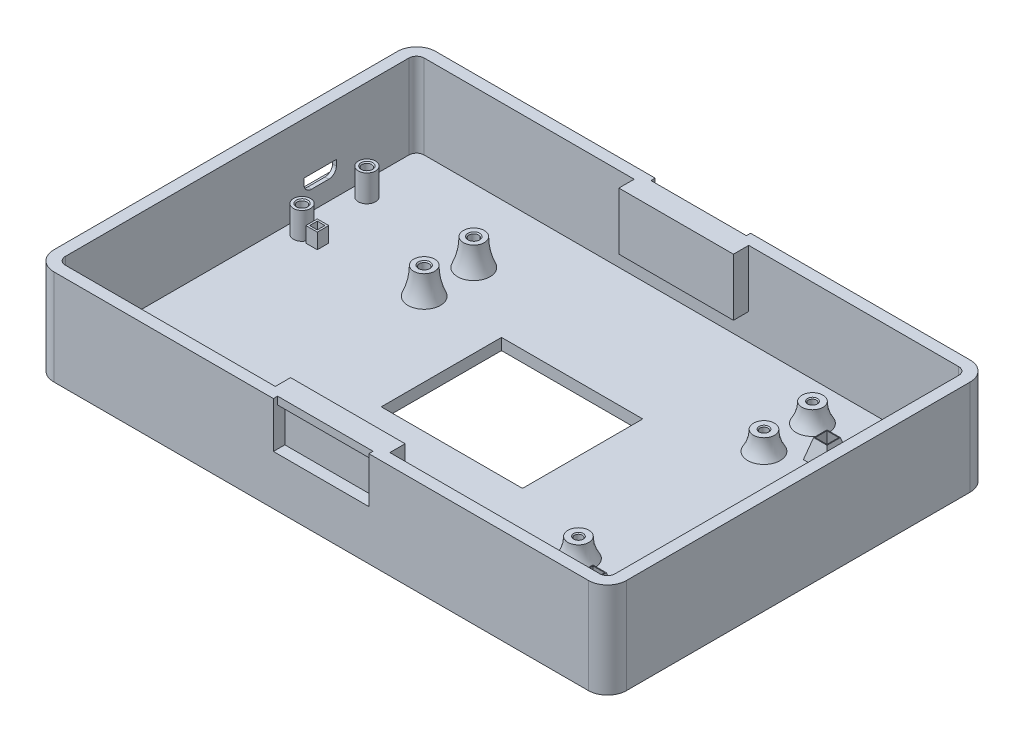
SolidWorks part; units mm, degrees
ref_plane "Front Plane" through (0, 0, 0) normal (0, 0, 1) x (1, 0, 0)
ref_plane "Top Plane" through (0, 0, 0) normal (0, 1, 0) x (1, 0, 0)
ref_plane "Right Plane" through (0, 0, 0) normal (1, 0, 0) x (0, 0, -1)
sketch "Sketch1" plane through (0, 0, 0) normal (0, 1, 0) x (1, 0, 0)
  line L1 (-75, -50) -> (75, -50)
  line L2 (-75, -50) -> (-75, 50)
  line L3 (-75, 50) -> (75, 50)
  line L4 (75, -50) -> (75, 50)
  point P4 (0, 50)
  point P6 (-75, 0)
  dimension "D1" = 100
  dimension "D2" = 150
extrude "Boss-Extrude1" add sketch "Sketch1" along normal blind 25
fillet "Fillet1" radius 5 4 edges at (75, 12.5, -50) (75, 12.5, 50) (-75, 12.5, 50) (-75, 12.5, -50)
shell "Shell2" thickness 3
sketch "Sketch4" plane through (0, 3, 0) normal (0, 1, 0) x (1, 0, 0)
  line L0 (41.7, 24.3) -> (62, 37) construction
  line L1 (41.7, 37) -> (62, 24.3) construction
  line L2 (62, 24.3) -> (62, 37) construction
  line L3 (62, 37) -> (41.7, 37) construction
  line L4 (41.7, 37) -> (41.7, 24.3) construction
  line L5 (41.7, 24.3) -> (62, 24.3) construction
  line L7 (70, 47) -> (-70, 47) construction
  line L8 (72, -45) -> (72, 45) construction
  circle A0 centre (62, 37) radius 2.25
  circle A1 centre (41.7, 37) radius 2.25
  circle A2 centre (41.7, 24.3) radius 2.25
  circle A3 centre (62, 24.3) radius 2.25
  dimension "D1" = 4.5
  dimension "D2" = 12.7
  dimension "D3" = 20.3
  dimension "D4" = 10
  dimension "D5" = 10
extrude "Boss-Extrude4" add sketch "Sketch4" along normal blind 5
hole_wizard "M2.5x0.45 Tapped Hole5" positions "Sketch11" profile "Sketch12" tap size "M2.5x0.45" standard "ANSI Metric"
sketch "Sketch11" plane through (0, 8, 0) normal (0, 1, 0) x (1, 0, 0)
  point P0 (41.7, 37)
  point P3 (62, 24.3)
  point P6 (62, 37)
  point P9 (41.7, 24.3)
sketch "Sketch12" plane through (41.7, 8, -37) normal (1, 0, 0) x (0, 0, 1)
  line L0 (0, 0) -> (0, 5.6159)
  line L1 (0, 5.6159) -> (1.025, 5)
  line L2 (1.025, 5) -> (1.025, 0.25)
  line L3 (1.025, 0.25) -> (1.275, 0)
  line L5 (1.275, 0) -> (0, 0)
  line L6 (-1.025, 0.25) -> (-1.275, 0) construction
  line L10 (0, 5.6159) -> (-1.025, 5) construction
  line L11 (0, -6.35) -> (0, 107.95) construction
  dimension "Tap Drill Dia." = 2.05
  dimension "Tap Drill Depth" = 5
  dimension "Near C'Sink Dia." = 2.55
  dimension "Near C'Sink Angle" = 90
  dimension "Drill Angle" = 118
cosmetic thread "Hole Thread1" parameters "D1"=5, "D2"=2.5
cosmetic thread "Hole Thread2" parameters "D1"=5, "D2"=2.5
cosmetic thread "Hole Thread3" parameters "D1"=5, "D2"=2.5
cosmetic thread "Hole Thread4" parameters "D1"=5, "D2"=2.5
ref_plane "Plane1" through (0, 8, 0) normal (0, 1, 0) x (1, 0, 0)
sketch "Sketch20" plane through (0, 8, 0) normal (0, 1, 0) x (1, 0, 0)
  line L0 (41.7, 24.3) -> (62, 37) construction
  line L1 (50.1, 28.9) -> (53.6, 28.9)
  line L2 (50.1, 28.9) -> (50.1, 32.4)
  line L3 (50.1, 32.4) -> (53.6, 32.4)
  line L4 (53.6, 28.9) -> (53.6, 32.4)
  line L5 (50.1, 28.9) -> (53.6, 32.4) construction
  line L6 (50.1, 32.4) -> (53.6, 28.9) construction
  point P0 (51.85, 30.65)
  dimension "D1" = 3.5
  dimension "D2" = 3.5
extrude "Boss-Extrude7" add sketch "Sketch20" against normal up to surface (5 mm away) draft 15
sketch "Sketch21" plane through (0, 8, 0) normal (0, 1, 0) x (1, 0, 0)
  line L0 (41.7, 24.3) -> (62, 37) construction
  line L1 (50.3, 29.1) -> (53.4, 29.1)
  line L2 (50.3, 29.1) -> (50.3, 32.2)
  line L3 (50.3, 32.2) -> (53.4, 32.2)
  line L4 (53.4, 29.1) -> (53.4, 32.2)
  line L5 (50.3, 29.1) -> (53.4, 32.2) construction
  line L6 (50.3, 32.2) -> (53.4, 29.1) construction
  point P0 (51.85, 30.65)
  dimension "D1" = 3.1
  dimension "D2" = 3.1
extrude "Cut-Extrude4" cut sketch "Sketch21" against normal through all draft 15 draft outward yes
sketch "Sketch22" plane through (0, 0, 0) normal (0, -1, 0) x (1, 0, 0)
  line L1 (-18.5, -15.75) -> (18.5, -15.75)
  line L2 (-18.5, -15.75) -> (-18.5, 15.75)
  line L3 (-18.5, 15.75) -> (18.5, 15.75)
  line L4 (18.5, -15.75) -> (18.5, 15.75)
  line L5 (-18.5, -15.75) -> (18.5, 15.75) construction
  line L6 (-18.5, 15.75) -> (18.5, -15.75) construction
  point P0 (0, 0)
  dimension "D1" = 31.5
  dimension "D2" = 37
extrude "Cut-Extrude6" cut sketch "Sketch22" against normal through all
sketch "Centerlines" plane through (0, 0, 0) normal (0, 1, 0) x (1, 0, 0)
  line L0 (0, 0) -> (96.0076, 0) construction
  line L1 (0, 0) -> (0, 57.905) construction
ref_plane "Plane2" through (0, 0, -37) normal (0, 0, 1) x (1, 0, 0)
sketch "Sketch24" plane through (0, 0, -37) normal (0, 0, 1) x (1, 0, 0)
  line L0 (43.95, 3) -> (45.95, 3)
  line L1 (43.95, 3) -> (43.95, 8)
  line L2 (43.95, 8) -> (44.45, 8)
  line L3 (44.45, 8) -> (44.45, 3) construction
  line L5 (41.7, 3) -> (41.7, 9.6112) construction
  arc A0 (44.45, 8) -> (45.95, 3) centre (53.5333, 8) ccw
  dimension "D1" = 0.5
  dimension "D2" = 2
revolve "Revolve1" add sketch "Sketch24" angle 360 about L5
pattern_linear "LPattern1" count 2 spacing 20.3 along (1, 0, 0) count 2 spacing 12.7 along (0, 0, 1) of "Revolve1"
mirror "Mirror1" about plane through (0, 0, 0) normal (0, 0, 1) of "LPattern1", "Boss-Extrude4", "M2.5x0.45 Tapped Hole5", "Boss-Extrude7", "Cut-Extrude4", "Revolve1"
cosmetic thread "Hole Thread5" parameters "D1"=5, "D2"=2.5
cosmetic thread "Hole Thread6" parameters "D1"=5, "D2"=2.5
cosmetic thread "Hole Thread7" parameters "D1"=5, "D2"=2.5
cosmetic thread "Hole Thread8" parameters "D1"=5, "D2"=2.5
sketch "Sketch25" plane through (0, 0, 0) normal (0, -1, 0) x (1, 0, 0)
  line L0 (70, -50) -> (-70, -50) construction
  line L1 (-69, -40) -> (-59, -40)
  line L2 (-69, -40) -> (-69, -20)
  line L4 (-59, -40) -> (-59, -20)
  line L5 (-69, -40) -> (-59, -20) construction
  line L6 (-69, -20) -> (-59, -40) construction
  line L8 (-68, -39) -> (-68, -21)
  line L13 (-68, -21) -> (-65, -21)
  line L14 (-60, -39) -> (-60, -21)
  line L15 (-68, -39) -> (-60, -39)
  line L17 (-69, -20) -> (-59, -20) construction
  line L18 (-63, -21) -> (-60, -21)
  line L20 (-65, -21) -> (-65, -20)
  line L21 (-65, -20) -> (-63, -20)
  line L22 (-63, -21) -> (-63, -20)
  line L23 (-68, -21) -> (-60, -21) construction
  line L24 (-69, -20) -> (-69, -19)
  line L25 (-59, -20) -> (-59, -19)
  line L26 (-59, -19) -> (-69, -19)
  line L27 (-75, -45) -> (-75, 45) construction
  point P0 (-64, -30)
  dimension "D1" = 10
  dimension "D2" = 20
  dimension "D3" = 20
  dimension "D4" = 6
  dimension "D5" = 1
  dimension "D6" = 1
  dimension "D7" = 1
  dimension "D8" = 2
extrude "Cut-Extrude7" cut sketch "Sketch25" against normal blind 1
sketch "Sketch26" plane through (0, 0, 0) normal (0, -1, 0) x (1, 0, 0)
  line L0 (-64, -21) -> (-64, -39) construction
  line L2 (-68, -39) -> (-60, -39) construction
  line L3 (-68, -30) -> (-60, -30) construction
  line L4 (-68, -21) -> (-68, -39) construction
  line L5 (-60, -39) -> (-60, -21) construction
  line L6 (-63.5, -24) -> (-66.5, -30.5)
  line L7 (-66.5, -30.5) -> (-64.5, -30.5)
  line L8 (-64.5, -30.5) -> (-64.5, -36)
  line L9 (-64.5, -36) -> (-62, -29.5)
  line L10 (-62, -29.5) -> (-63.5, -29.5)
  line L11 (-63.5, -29.5) -> (-63.5, -24)
  line L12 (-68, -21) -> (-60, -21) construction
  dimension "D1" = 0.5
  dimension "D2" = 0.5
  dimension "D3" = 0.5
  dimension "D4" = 0.5
  dimension "D5" = 2
  dimension "D6" = 2
  dimension "D7" = 6
  dimension "D8" = 6
extrude "Cut-Extrude8" cut sketch "Sketch26" against normal blind 1
sketch "Sketch27" plane through (0, 0, 0) normal (0, -1, 0) x (1, 0, 0)
  line L0 (-59, -19) -> (-69, -19) construction
  line L1 (-65, -14) -> (-63, -14)
  line L2 (-65, -14) -> (-65, -12)
  line L3 (-65, -12) -> (-63, -12)
  line L4 (-63, -14) -> (-63, -12)
  line L5 (-59, -19) -> (-69, -19) construction
  point P6 (-64, -14)
  point P7 (-64, -19)
  dimension "D1" = 5
  dimension "D2" = 2
  dimension "D3" = 2
extrude "Cut-Extrude9" cut sketch "Sketch27" against normal through all
sketch "Sketch28" plane through (0, 3, 0) normal (0, 1, 0) x (1, 0, 0)
  line L0 (-65.5, 11.5) -> (-65.5, 14.5)
  line L1 (-65, 12) -> (-63, 12)
  line L2 (-65, 12) -> (-65, 14)
  line L3 (-65, 14) -> (-63, 14)
  line L4 (-63, 12) -> (-63, 14)
  line L5 (-65.5, 14.5) -> (-62.5, 14.5)
  line L6 (-62.5, 11.5) -> (-62.5, 14.5)
  line L7 (-65.5, 11.5) -> (-62.5, 11.5)
  dimension "D1" = 0.5
extrude "Boss-Extrude8" add sketch "Sketch28" along normal blind 4
sketch "Sketch29" plane through (0, 3, 0) normal (0, 1, 0) x (1, 0, 0)
  line L0 (-63, 12) -> (-63, 14) construction
  line L1 (-63, 12) -> (-63, 14) construction
  line L2 (-38, 28) -> (-38, 15) construction
  line L3 (-68, 30) -> (-68, 13) construction
  circle A0 centre (-68, 30) radius 2.25
  circle A1 centre (-38, 28) radius 2.25
  circle A2 centre (-38, 15) radius 2.25
  circle A3 centre (-68, 13) radius 2.25
  point P8 (-68, 21.5)
  point P9 (-38, 21.5)
  point P13 (-63, 13)
  dimension "D1" = 4.5
  dimension "D2" = 30
  dimension "D3" = 5
  dimension "D4" = 13
  dimension "D5" = 17
extrude "Boss-Extrude9" add sketch "Sketch29" along normal blind 7
hole_wizard "M3x0.5 Tapped Hole2" positions "Sketch30" profile "Sketch31" tap size "M3x0.5" standard "ANSI Metric"
sketch "Sketch30" plane through (0, 10, 0) normal (0, 1, 0) x (1, 0, 0)
  point P0 (-68, 30)
  point P3 (-38, 28)
  point P6 (-38, 15)
  point P9 (-68, 13)
sketch "Sketch31" plane through (-68, 10, -30) normal (1, 0, 0) x (0, 0, 1)
  line L0 (0, 0) -> (0, 7.7511)
  line L1 (0, 7.7511) -> (1.25, 7)
  line L2 (1.25, 7) -> (1.25, 0.275)
  line L3 (1.25, 0.275) -> (1.525, 0)
  line L5 (1.525, 0) -> (0, 0)
  line L6 (-1.25, 0.275) -> (-1.525, 0) construction
  line L10 (0, 7.7511) -> (-1.25, 7) construction
  line L11 (0, -6.35) -> (0, 107.95) construction
  dimension "Tap Drill Dia." = 2.5
  dimension "Tap Drill Depth" = 7
  dimension "Near C'Sink Dia." = 3.05
  dimension "Near C'Sink Angle" = 90
  dimension "Drill Angle" = 118
cosmetic thread "Hole Thread9" parameters "D1"=6, "D2"=3
cosmetic thread "Hole Thread10" parameters "D1"=6, "D2"=3
cosmetic thread "Hole Thread11" parameters "D1"=6, "D2"=3
cosmetic thread "Hole Thread12" parameters "D1"=6, "D2"=3
sketch "Sketch32" plane through (-72, 0, 0) normal (1, 0, 0) x (0, 0, -1)
  line L1 (19.5, 8) -> (24, 8)
  line L2 (17.5, 10) -> (17.5, 11.5)
  line L3 (17.5, 11.5) -> (26, 11.5)
  line L4 (26, 10) -> (26, 11.5)
  line L5 (15.25, 10) -> (10.75, 10) construction
  line L6 (32.25, 10) -> (27.75, 10) construction
  line L7 (32.25, 10) -> (27.75, 10) construction
  line L8 (15.25, 10) -> (10.75, 10) construction
  arc A0 (17.5, 10) -> (19.5, 8) centre (19.5, 10) ccw
  arc A1 (26, 10) -> (24, 8) centre (24, 10) cw
  dimension "D1" = 8.5
  dimension "D2" = 4.5
  dimension "D3" = 2
  dimension "D4" = 2
  dimension "D5" = 2
  dimension "D6" = 3.5
  dimension "D7" = 1.5
extrude "Cut-Extrude10" cut sketch "Sketch32" against normal through all
sketch "Sketch33" plane through (-75, 27.8648, -44.5406) normal (-1, 0, 0) x (0, 0, -1)
  line L1 (-18.5406, 16.3648) -> (-27.0406, 16.3648) construction
  line L3 (-18.5406, 17.8648) -> (-18.5406, 16.3648) construction
  text T0 "PWR"
  dimension "D1" = 7
  dimension "D2" = 9
extrude "Cut-Extrude12" cut sketch "Sketch33" against normal blind 1
ref_plane "Plane3" through (0, 0, -28) normal (0, 0, 1) x (1, 0, 0)
sketch "Sketch34" plane through (0, 0, -28) normal (0, 0, 1) x (1, 0, 0)
  line L0 (-35.75, 10) -> (-35.25, 10)
  line L1 (-35.75, 3) -> (-40.25, 3) construction
  line L2 (-35.75, 3) -> (-40.25, 3) construction
  line L3 (-35.75, 10) -> (-35.75, 3)
  line L4 (-35.75, 3) -> (-33.75, 3)
  line L5 (-38, 4.1191) -> (-38, 22.0692) construction
  arc A0 (-35.25, 10) -> (-33.75, 3) centre (-18.1667, 10) ccw
  dimension "D1" = 0.5
  dimension "D2" = 2
revolve "Revolve2" add sketch "Sketch34" angle 360 about L5
sketch "Sketch36" plane through (0, 3, 0) normal (0, 1, 0) x (1, 0, 0)
  line L0 (-38, 28) -> (-38, 15) construction
  line L1 (-38, 21.5) -> (-96.3711, 21.5) construction
ref_plane "Plane4" through (0, 0, -21.5) normal (0, 0, 1) x (1, 0, 0)
mirror "Mirror2" about plane through (0, 0, -21.5) normal (0, 0, 1) of "Revolve2"
sketch "Sketch38" plane through (0, 0, -50) normal (0, 0, -1) x (-1, 0, 0)
  line L0 (-70, 25) -> (70, 25) construction
  line L1 (-15, 25) -> (15, 25)
  line L2 (-15, 25) -> (-15, 10)
  line L3 (-15, 10) -> (15, 10)
  line L4 (15, 25) -> (15, 10)
  point P6 (0, 10)
  dimension "D1" = 30
  dimension "D2" = 15
extrude "Boss-Extrude10" add sketch "Sketch38" against normal blind 7
sketch "Sketch39" plane through (0, 0, -50) normal (0, 0, -1) x (-1, 0, 0)
  line L0 (-70, 25) -> (70, 25) construction
  line L1 (-12.5, 13) -> (12.5, 13)
  line L2 (-12.5, 13) -> (-12.5, 23)
  line L3 (-12.5, 23) -> (12.5, 23)
  line L4 (12.5, 13) -> (12.5, 23)
  point P4 (0, 13)
  dimension "D1" = 2
  dimension "D2" = 25
  dimension "D3" = 10
extrude "Cut-Extrude13" cut sketch "Sketch39" against normal blind 3
sketch "Sketch40" plane through (0, 0, -50) normal (0, 0, -1) x (-1, 0, 0)
  line L0 (-70, 25) -> (70, 25) construction
  line L1 (-12.5, 23) -> (12.5, 23)
  line L2 (-12.5, 23) -> (-12.5, 25)
  line L3 (-12.5, 25) -> (12.5, 25)
  line L4 (12.5, 23) -> (12.5, 25)
  line L5 (12.5, 13) -> (12.5, 23) construction
extrude "Cut-Extrude14" cut sketch "Sketch40" against normal blind 1.1
mirror "Mirror3" about plane through (0, 0, 0) normal (0, 0, 1) of "Cut-Extrude14", "Cut-Extrude13", "Boss-Extrude10"
sketch "Sketch41" plane through (0, 0, 0) normal (0, -1, 0) x (1, 0, 0)
  line L0 (21.5, 50) -> (21.5, -50) construction
  line L1 (-70, 50) -> (70, 50) construction
  line L2 (70, -50) -> (-70, -50) construction
  line L5 (18.5, -15.75) -> (18.5, 15.75) construction
  text T0 "Plant Health Tracker" font "Century Gothic" height in points 18
  dimension "D1" = 3
extrude "Cut-Extrude15" cut sketch "Sketch41" against normal blind 1
sketch "Sketch42" plane through (0, 0, 0) normal (0, -1, 0) x (1, 0, 0)
  line L0 (18.5, -15.75) -> (18.5, 15.75) construction
  line L1 (-41.5, 7.5) -> (-21.5, 7.5) construction
  line L2 (-41.5, 7.5) -> (-41.5, -7.5) construction
  line L3 (-41.5, -7.5) -> (-21.5, -7.5) construction
  line L4 (-21.5, 7.5) -> (-21.5, -7.5) construction
  line L5 (18.5, -15.75) -> (18.5, 15.75) construction
  line L6 (-36.3, 6.92) -> (-35.5, 7.2553) construction
  line L7 (-18.5, 15.75) -> (-18.5, -15.75) construction
  arc A10 (-41.5, 7) -> (-35.5, 7.2553) centre (-37.9772, -5.16) cw
  arc A11 (-41.5, 7) -> (-36.3, 6.92) centre (-39.1118, -6.807) cw
  arc A12 (-35.5, 7.2553) -> (-22, -7.5) centre (-33.127, -4.127) cw
  arc A13 (-34.2605, 6.9421) -> (-25.3602, -4.118) centre (-37.9772, -5.16) cw
  arc A14 (-22, -7.5) -> (-24.8, -5.4543) centre (-25.023, -8.6986) ccw
  arc A15 (-24.8, -5.4543) -> (-36.3, 6.92) centre (-23.9533, 6.8634) cw
  arc A16 (-22.2, -6.2272) -> (-24.7657, -4.9555) centre (-25.023, -8.6986) ccw
  arc A17 (-24.7657, -4.9555) -> (-35.8, 6.808) centre (-23.9533, 6.8634) cw
  arc A18 (-35.398, 6.7658) -> (-22.2, -6.2272) centre (-33.127, -4.127) cw construction
  arc A19 (-34.2605, 6.9421) -> (-22.2, -6.2272) centre (-33.127, -4.127) cw
  arc A20 (-24.7657, -4.9555) -> (-35.8, 6.9177) centre (-23.9533, 6.8634) cw construction
  arc A21 (-35.8, 6.808) -> (-25.3602, -4.118) centre (-39.1118, -6.807) cw
  point P6 (18.5, 0)
  point P7 (-41.5, 0)
  dimension "D6" = 2
  dimension "D10" = 0.5
  dimension "D11" = 5.7
  dimension "D1" = 15
  dimension "D2" = 20
  dimension "D3" = 3
  dimension "D4" = 0.5
  dimension "D5" = 5.2
  dimension "D7" = 0.5
  dimension "D8" = 6
  dimension "D9" = 0.58
  dimension "D12" = 0.7
  dimension "D13" = 16.7
extrude "Cut-Extrude16" cut sketch "Sketch42" against normal blind 1
sketch "Sketch43" plane through (-75, 0, 0) normal (-1, 0, 0) x (0, 0, 1)
  line L0 (-26.8694, 10.05) -> (-16.3694, 10.05) construction
  line L1 (-26.8694, 10.05) -> (-16.3694, 10.05) construction
  line L2 (-26.8694, 13.6) -> (-16.3694, 13.6)
  line L3 (-26.8694, 6.5) -> (-16.3694, 6.5)
  line L4 (-26, 11.5) -> (-17.5, 11.5) construction
  line L5 (-26, 11.5) -> (-17.5, 11.5) construction
  arc A0 (-26.8694, 13.6) -> (-26.8694, 6.5) centre (-26.8694, 10.05) ccw
  arc A1 (-16.3694, 6.5) -> (-16.3694, 13.6) centre (-16.3694, 10.05) ccw
  point P2 (-21.6194, 10.05)
  dimension "D1" = 7.1
  dimension "D2" = 10.5
  dimension "D3" = 5
extrude "Cut-Extrude17" cut sketch "Sketch43" against normal blind 2
